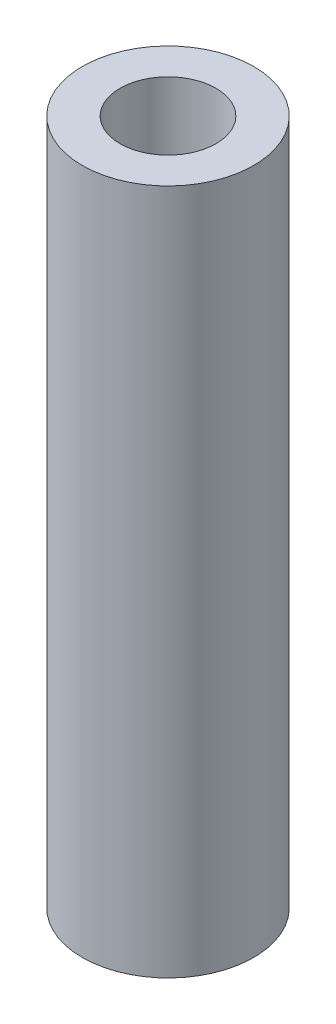
SolidWorks part; units mm, degrees
ref_plane "Front Plane" through (0, 0, 0) normal (0, 0, 1) x (1, 0, 0)
ref_plane "Top Plane" through (0, 0, 0) normal (0, 1, 0) x (1, 0, 0)
ref_plane "Right Plane" through (0, 0, 0) normal (1, 0, 0) x (0, 0, -1)
sketch "Sketch1" plane through (0, 0, 0) normal (0, 1, 0) x (1, 0, 0)
  circle A0 centre (0, 0) radius 2.5
  circle A1 centre (0, 0) radius 1.4
  dimension "D1" = 5
  dimension "D2" = 2.8
extrude "Boss-Extrude1" add sketch "Sketch1" along normal blind 20
